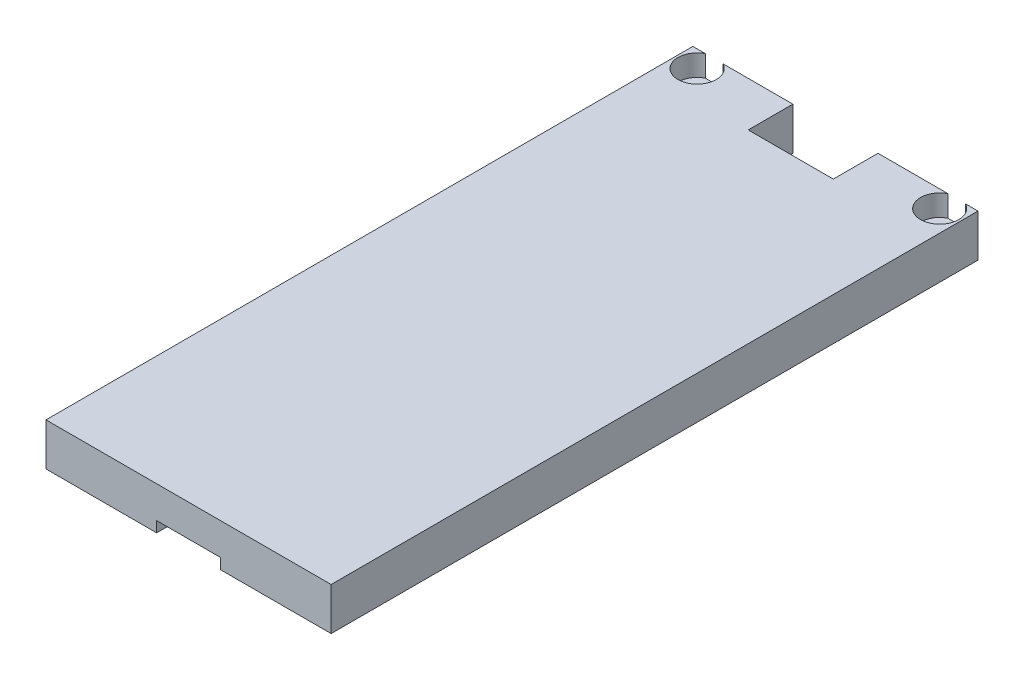
SolidWorks part; units mm, degrees
ref_plane "Front Plane" through (0, 0, 0) normal (0, 0, 1) x (1, 0, 0)
ref_plane "Top Plane" through (0, 0, 0) normal (0, 1, 0) x (1, 0, 0)
ref_plane "Right Plane" through (0, 0, 0) normal (1, 0, 0) x (0, 0, -1)
sketch "Sketch1" plane through (0, 0, 0) normal (0, 0, 1) x (1, 0, 0)
  line L0 (-33.5, 0) -> (-33.5, 10)
  line L9 (-33.5, 10) -> (33.5, 10)
  line L10 (33.5, 10) -> (33.5, 0)
  line L11 (33.5, 0) -> (7.5, 0)
  line L12 (7.5, 0) -> (7.5, 2.5)
  line L13 (7.5, 2.5) -> (-7.5, 2.5)
  line L14 (-7.5, 2.5) -> (-7.5, 0)
  line L15 (-7.5, 0) -> (-33.5, 0)
  line L16 (0, 0) -> (0, 23.0948) construction
  point P2 (0, 10)
  dimension "D1" = 67
  dimension "D2" = 10
  dimension "D3" = 15
  dimension "D4" = 2.5
extrude "Boss-Extrude1" add sketch "Sketch1" along normal blind 152
sketch "Sketch2" plane through (0, 10, 0) normal (0, 1, 0) x (1, 0, 0)
  line L0 (33.5, 0) -> (-33.5, 0) construction
  line L1 (-10, 0) -> (10, 0)
  line L2 (-10, 0) -> (-10, -10.5)
  line L3 (-10, -10.5) -> (10, -10.5)
  line L4 (10, 0) -> (10, -10.5)
  line L5 (0, -0.6348) -> (0, 12.5514) construction
  point P6 (0, 0)
  dimension "D1" = 20
  dimension "D2" = 10.5
extrude "Cut-Extrude1" cut sketch "Sketch2" against normal through all
sketch "Sketch6" plane through (0, 10, 0) normal (0, 1, 0) x (1, 0, 0)
  line L0 (-10, 0) -> (-33.5, 0) construction
  line L1 (-10, 0) -> (-10, -10.5) construction
  arc A1 (-30.56, 0) -> (-26.44, 0) centre (-28.5, -4.0008) ccw
  point P2 (-27.0701, 0)
  line M4 (-10, 0) -> (-33.5, 0)
  dimension "D2" = 4.5
  dimension "D3" = 4.12
  dimension "D4" = 18.5
extrude "Cut-Extrude2" cut sketch "Sketch6" against normal blind 5 contours A1 M4
sketch "Sketch7" plane through (0, 5, 0) normal (0, 1, 0) x (1, 0, 0)
  circle A0 centre (-28.5, -4.0008) radius 2.6
  dimension "D1" = 5.2
extrude "Cut-Extrude3" cut sketch "Sketch7" against normal through all
mirror "Mirror1" about plane through (0, 0, 0) normal (1, 0, 0) of "Cut-Extrude3", "Cut-Extrude2"
